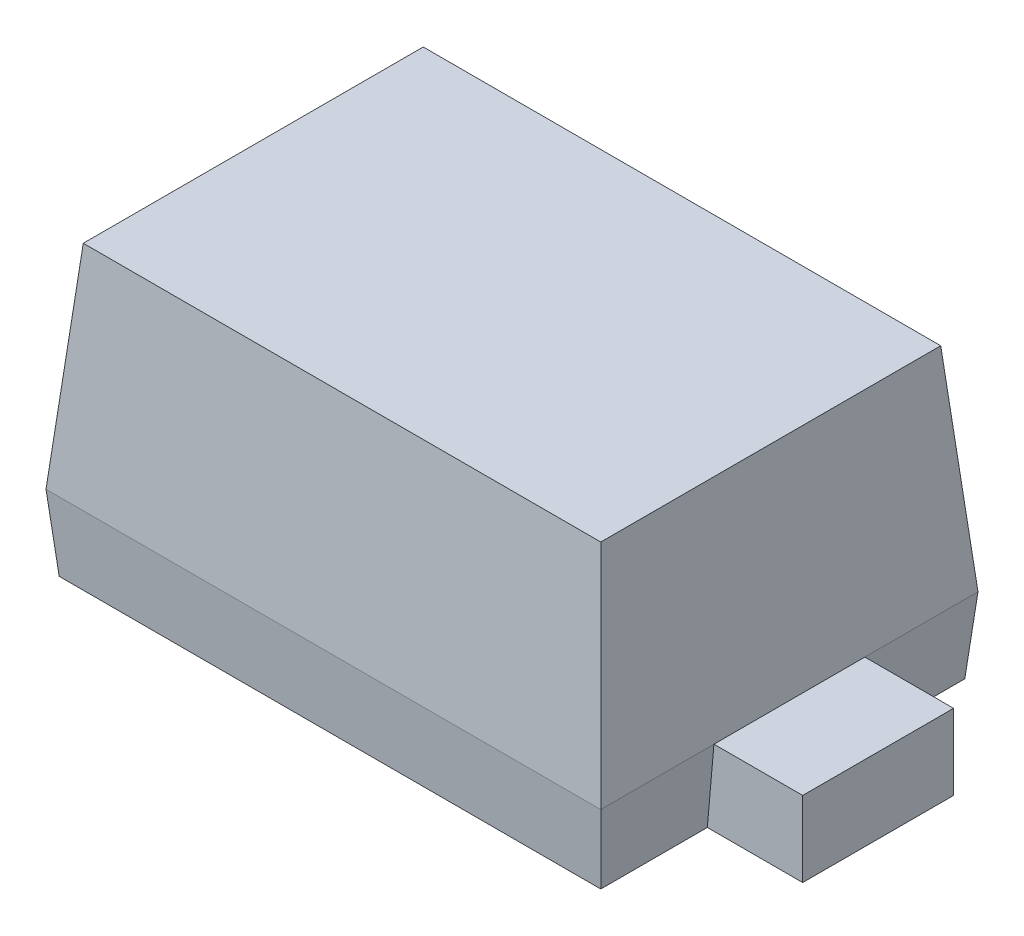
SolidWorks part; units mm, degrees
ref_plane "Front Plane" through (0, 0, 0) normal (0, 0, 1) x (1, 0, 0)
ref_plane "Top Plane" through (0, 0, 0) normal (0, 1, 0) x (1, 0, 0)
ref_plane "Right Plane" through (0, 0, 0) normal (1, 0, 0) x (0, 0, -1)
sketch "Sketch1" plane through (0, 0, 0) normal (0, 1, 0) x (1, 0, 0)
  line L1 (-0.625, -0.425) -> (0.625, -0.425)
  line L2 (-0.625, -0.425) -> (-0.625, 0.425)
  line L3 (-0.625, 0.425) -> (0.625, 0.425)
  line L4 (0.625, -0.425) -> (0.625, 0.425)
  line L5 (-0.625, -0.425) -> (0.625, 0.425) construction
  line L6 (-0.625, 0.425) -> (0.625, -0.425) construction
  point P0 (0, 0)
  dimension "D1" = 1.25
  dimension "D2" = 0.85
extrude "Boss-Extrude1" add sketch "Sketch1" along normal blind 0.48 draft 5 and the other way blind 0.17 draft 5
ref_plane "Plane1" through (0, 0, 0) normal (0, 0, 1) x (1, 0, 0)
ref_plane "Plane2" through (0, 0, 0) normal (-1, 0, 0) x (0, 0, 1)
sketch "Sketch2" plane through (0, 0, 0) normal (0, 0, 1) x (1, 0, 0)
  line L0 (0.7761, 0) -> (0.5995, 0)
  line L2 (0.5995, 0) -> (0.5995, -0.575)
  line L3 (0.5995, -0.575) -> (0.9995, -0.575)
  dimension "D1" = 0.4
sketch "Sketch4" plane through (0, -0.17, 0) normal (0, -1, 0) x (1, 0, 0)
  line L0 (-0.625, -0.17) -> (-0.583, -0.17)
  line L1 (-0.625, -0.425) -> (-0.625, 0.425) construction
  line L2 (-0.583, -0.383) -> (-0.583, 0.383) construction
  line L3 (0.625, 0.425) -> (0.625, -0.425) construction
  line L4 (0.625, -0.17) -> (0.825, -0.17)
  line L6 (0.625, 0.17) -> (0.825, 0.17)
  line L7 (-0.825, -0.17) -> (-0.625, -0.17)
  line L8 (-0.825, -0.17) -> (-0.825, 0.17)
  line L9 (-0.825, 0.17) -> (-0.625, 0.17)
  line L10 (0.625, -0.17) -> (0.583, -0.17)
  line L11 (0.825, -0.17) -> (0.825, 0.17)
  line L12 (-0.583, -0.17) -> (-0.583, 0.17)
  line L13 (-0.583, 0.17) -> (-0.625, 0.17)
  line L14 (0.583, 0.383) -> (0.583, -0.383) construction
  line L15 (0.583, -0.17) -> (0.583, 0.17)
  line L16 (0.583, 0.17) -> (0.625, 0.17)
extrude "Boss-Extrude2" add sketch "Sketch4" against normal blind 0.17
sketch "Bend-Lines1" plane through (0, 0, 0) normal (0, 1, 0) x (1, 0, 0)
sketch "Bounding-Box1" plane through (0, 0, 0) normal (0, 1, 0) x (1, 0, 0)
